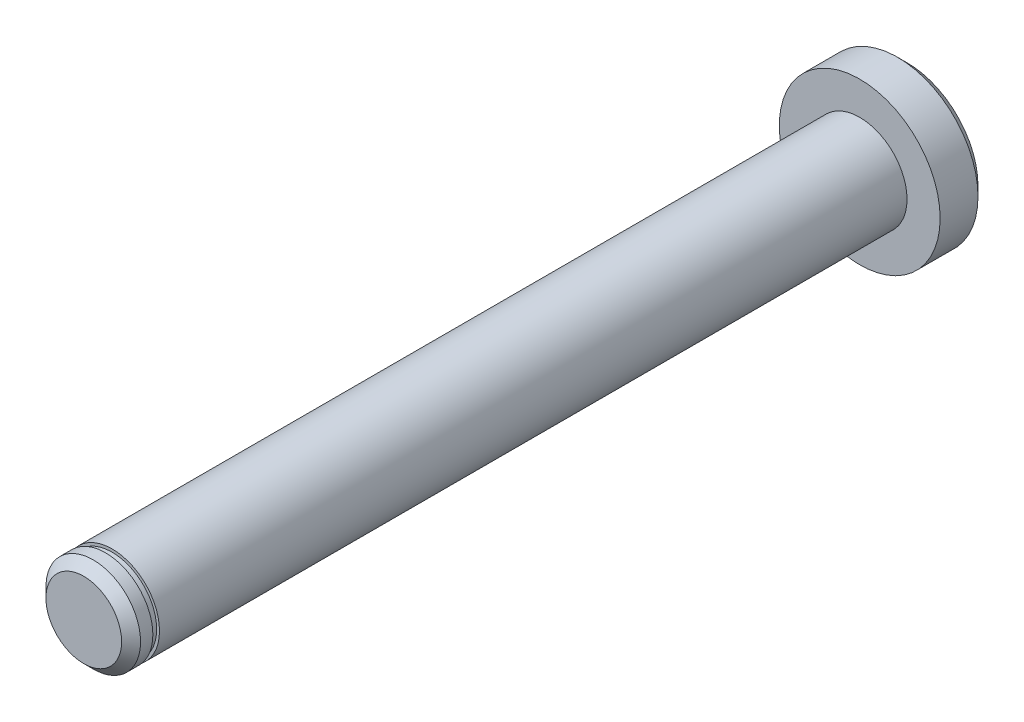
SolidWorks part; units mm, degrees
ref_plane "Front Plane" through (0, 0, 0) normal (0, 0, 1) x (1, 0, 0)
ref_plane "Top Plane" through (0, 0, 0) normal (0, 1, 0) x (1, 0, 0)
ref_plane "Right Plane" through (0, 0, 0) normal (1, 0, 0) x (0, 0, -1)
sketch "Sketch1" plane through (0, 0, 0) normal (0, 0, 1) x (1, 0, 0)
  circle A0 centre (0, 0) radius 8.5
  dimension "D1" = 17
extrude "Boss-Extrude1" add sketch "Sketch1" along normal blind 5
sketch "Sketch2" plane through (0, 0, 5) normal (0, 0, 1) x (1, 0, 0)
  circle A0 centre (0, 0) radius 5
  dimension "D1" = 10
extrude "Boss-Extrude2" add sketch "Sketch2" along normal blind 82
chamfer "Chamfer1" distance 1 angle 45 2 edges at (8.5, 0, 0) (5, 0, 87)
ref_plane "Plane1" through (0, 0, 84) normal (0, 0, 1) x (1, 0, 0)
sketch "Sketch3" plane through (0, 0, 84) normal (0, 0, 1) x (1, 0, 0)
  circle A0 centre (0, 0) radius 4.7
  dimension "D1" = 9.4
extrude "Cut-Extrude-Thin1" cut sketch "Sketch3" along normal blind 0.7 thin
